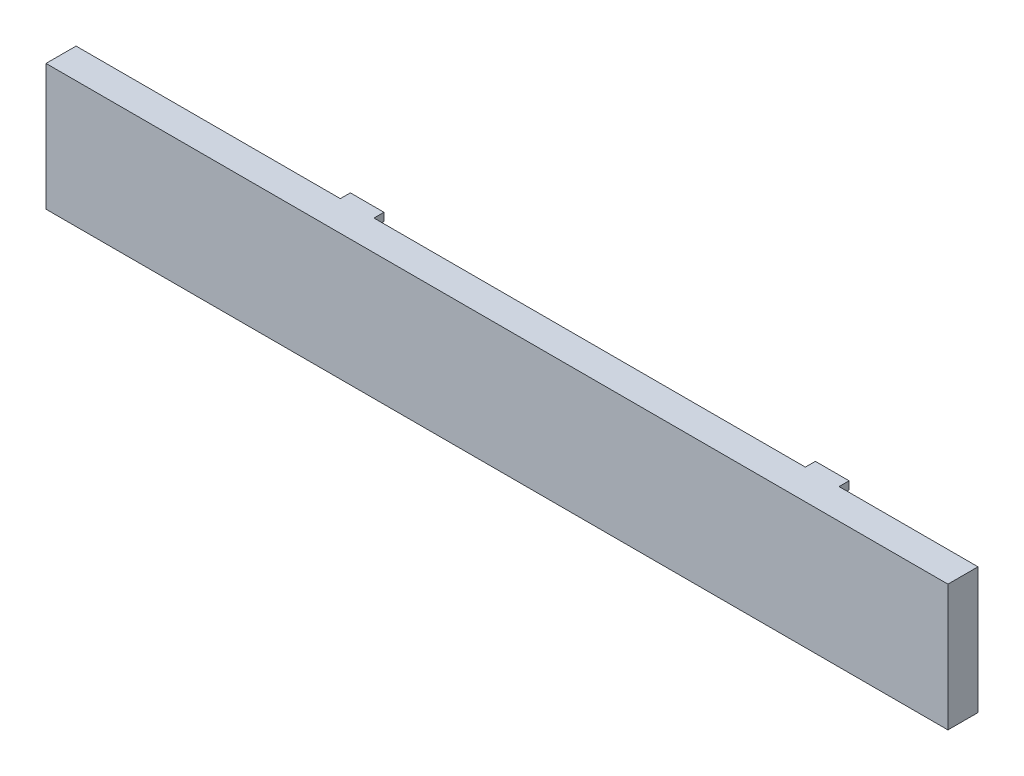
SolidWorks part; units mm, degrees
material "尼龙 101"
ref_plane "前视基准面" through (0, 0, 0) normal (0, 0, 1) x (1, 0, 0)
ref_plane "上视基准面" through (0, 0, 0) normal (0, 1, 0) x (1, 0, 0)
ref_plane "右视基准面" through (0, 0, 0) normal (1, 0, 0) x (0, 0, -1)
other "Configuration Table"
sketch "草图1" plane through (0, 0, 0) normal (0, 0, 1) x (1, 0, 0)
  line L1 (-1271.2202, 856.4324) -> (-821.2202, 856.4324)
  line L2 (-1271.2202, 856.4324) -> (-1271.2202, 793.4324)
  line L3 (-1271.2202, 793.4324) -> (-821.2202, 793.4324)
  line L4 (-821.2202, 856.4324) -> (-821.2202, 793.4324)
  dimension "D1" = 450
  dimension "D2" = 63
extrude "凸台-拉伸1" add sketch "草图1" along normal blind 20
sketch "草图2" plane through (0, 0, 20) normal (0, 0, 1) x (1, 0, 0)
  line L0 (-1271.2202, 856.4324) -> (-1271.2202, 793.4324) construction
  line L1 (-1271.2202, 852.4324) -> (-826.2202, 852.4324)
  line L2 (-1271.2202, 852.4324) -> (-1271.2202, 797.4324)
  line L3 (-1271.2202, 797.4324) -> (-826.2202, 797.4324)
  line L4 (-826.2202, 852.4324) -> (-826.2202, 797.4324)
  line L5 (-821.2202, 793.4324) -> (-821.2202, 856.4324) construction
  line L6 (-821.2202, 856.4324) -> (-1271.2202, 856.4324) construction
  line L7 (-1271.2202, 793.4324) -> (-821.2202, 793.4324) construction
  point P8 (-821.2202, 824.9324)
  point P9 (-826.2202, 824.9324)
  dimension "D1" = 4
  dimension "D2" = 4
  dimension "D3" = 5
extrude "切除-拉伸1" cut sketch "草图2" along normal blind 10 from surface at -20 starting at face at (-1046.2202, 824.9324, 0)
sketch "草图3" plane through (0, 793.4324, 0) normal (0, -1, 0) x (1, 0, 0)
  line L0 (-1271.2202, 20) -> (-1271.2202, 0) construction
  line L1 (-1271.2202, 5) -> (-1139.3715, 5)
  line L2 (-1271.2202, 5) -> (-1271.2202, 0)
  line L3 (-1271.2202, 0) -> (-1139.3715, 0)
  line L4 (-1139.3715, 5) -> (-1139.3715, 0)
  line L5 (-1271.2202, 0) -> (-821.2202, 0) construction
  line L7 (-1122.5981, 5) -> (-907.3603, 5)
  line L8 (-1122.5981, 5) -> (-1122.5981, 0)
  line L9 (-1122.5981, 0) -> (-907.3603, 0)
  line L10 (-907.3603, 5) -> (-907.3603, 0)
  line L11 (-890.5447, 5) -> (-821.2202, 5)
  line L12 (-890.5447, 5) -> (-890.5447, 0)
  line L13 (-890.5447, 0) -> (-821.2202, 0)
  line L14 (-821.2202, 5) -> (-821.2202, 0)
  dimension "D1" = 5
  dimension "D2" = 5
  dimension "D3" = 5
extrude "切除-拉伸2" cut sketch "草图3" against normal through all
